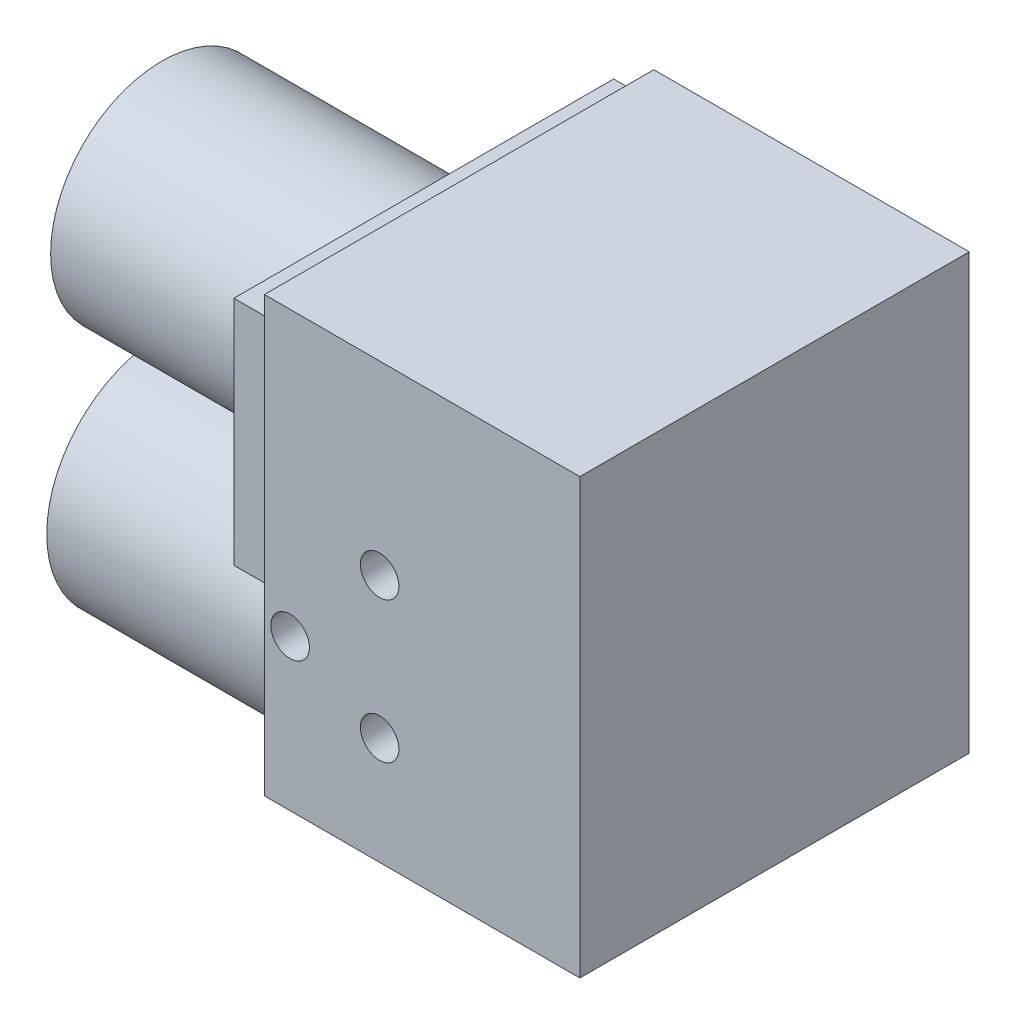
SolidWorks part; units mm, degrees
ref_plane "Front Plane" through (0, 0, 0) normal (0, 0, 1) x (1, 0, 0)
ref_plane "Top Plane" through (0, 0, 0) normal (0, 1, 0) x (1, 0, 0)
ref_plane "Right Plane" through (0, 0, 0) normal (1, 0, 0) x (0, 0, -1)
sketch "Sketch2" plane through (0, 0, 0) normal (0, 0, 1) x (1, 0, 0)
  line L1 (-49.09, 67.575) -> (49.09, 67.575)
  line L2 (-49.09, 67.575) -> (-49.09, -67.575)
  line L3 (-49.09, -67.575) -> (49.09, -67.575)
  line L4 (49.09, 67.575) -> (49.09, -67.575)
  point P4 (0, 67.575)
  point P6 (-49.09, 0)
  dimension "D1" = 135.15
  dimension "D2" = 98.18
extrude "Boss-Extrude1" add sketch "Sketch2" along normal blind 55.6 and the other way blind 65.6
sketch "Sketch3" plane through (-49.09, 0, 0) normal (-1, 0, 0) x (0, 0, 1)
  line L0 (-65.6, 67.575) -> (55.6, 67.575) construction
  circle A0 centre (0, 24.325) radius 34.65
  circle A1 centre (0, -50.675) radius 35.85
  point P4 (0, 0)
  point P8 (0, -38.3038)
  point P10 (0, 0)
  point P11 (-5, 24.575)
  point P12 (0, 0)
  point P13 (-5, 24.575)
  point P14 (-5, 24.575)
  point P15 (-5, 87.2668)
  point P16 (0, 0)
  point P17 (0, 0)
  point P18 (0, 18.7737)
  point P19 (0, 0)
  point P20 (0, 0)
  dimension "D1" = 69.3
  dimension "D3" = 75
  dimension "D4" = 71.7
  dimension "D2" = 43.25
extrude "Boss-Extrude2" add sketch "Sketch3" along normal blind 87.5
hole_wizard "Tap Drill for M14x2.0 Tap1" positions "Sketch5" profile "Sketch4" hole size "M14x2.0" standard "ANSI Metric"
sketch "Sketch5" plane through (0, 0, 55.6) normal (0, 0, 1) x (1, 0, 0)
  line L0 (-49.09, -67.575) -> (49.09, -67.575) construction
  line L1 (-49.09, 67.575) -> (-49.09, -67.575) construction
  point P0 (-13.23, 9.825)
  point P1 (-13.23, -34.075)
  point P3 (-41.09, -20.575)
  point P6 (10.8119, 15.3653)
  point P7 (0, 0)
  point P12 (0, 0)
  point P13 (0, -67.575)
  point P14 (0, 0)
  dimension "D1" = 33.5
  dimension "D2" = 35.86
  dimension "D3" = 77.4
  dimension "D4" = 8
  dimension "D5" = 47
sketch "Sketch4" plane through (-13.23, 9.825, 55.6) normal (1, 0, 0) x (0, -1, 0)
  line L0 (0, 0) -> (0, 23.1652)
  line L1 (0, 23.1652) -> (6, 19.56)
  line L2 (6, 19.56) -> (6, 0)
  line L5 (6, 0) -> (0, 0)
  line L10 (0, 23.1652) -> (-6, 19.56) construction
  line L11 (0, -6.35) -> (0, 107.95) construction
  dimension "Hole Dia." = 12
  dimension "Hole Depth" = 19.56
  dimension "Drill Angle" = 118
hole_wizard "Tap Drill for M12x1.5 Tap2" positions "Sketch6" profile "Sketch7" hole size "M12x1.5" standard "ANSI Metric"
sketch "Sketch6" plane through (0, -67.575, 0) normal (0, -1, 0) x (-1, 0, 0)
  line L0 (49.09, -55.6) -> (-49.09, -55.6) construction
  line L1 (49.09, -31.6166) -> (49.09, -55.6) construction
  line L2 (49.09, 65.6) -> (49.09, 31.6166) construction
  line L3 (49.09, 65.6) -> (-49.09, 65.6) construction
  point P0 (32.79, -35.1)
  point P2 (36.39, 57.2)
  dimension "D1" = 20.5
  dimension "D2" = 16.3
  dimension "D3" = 12.7
  dimension "D4" = 8.4
sketch "Sketch7" plane through (-32.79, -67.575, 35.1) normal (1, 0, 0) x (0, 0, -1)
  line L0 (0, 0) -> (0, 22.7145)
  line L1 (0, 22.7145) -> (5.25, 19.56)
  line L2 (5.25, 19.56) -> (5.25, 0)
  line L5 (5.25, 0) -> (0, 0)
  line L10 (0, 22.7145) -> (-5.25, 19.56) construction
  line L11 (0, -6.35) -> (0, 107.95) construction
  dimension "Hole Dia." = 10.5
  dimension "Hole Depth" = 19.56
  dimension "Drill Angle" = 118
sketch "Sketch8" plane through (-49.09, 0, 0) normal (-1, 0, 0) x (0, 0, 1)
  line L0 (55.6, 67.575) -> (55.6, -67.575) construction
  line L1 (-64.1, 60.325) -> (54.1, 60.325)
  line L2 (-64.1, 60.325) -> (-64.1, -11.675)
  line L3 (-64.1, -11.675) -> (54.1, -11.675)
  line L4 (54.1, 60.325) -> (54.1, -11.675)
  line L5 (-65.6, 67.575) -> (-65.6, -67.575) construction
  line L6 (-65.6, 67.575) -> (55.6, 67.575) construction
  circle A0 centre (0, 24.325) radius 34.65 construction
  circle A1 centre (0, 24.325) radius 34.65 construction
  dimension "D2" = 36
  dimension "D1" = 36
  dimension "D3" = 1.5
  dimension "D4" = 1.5
  dimension "D5" = 7.25
extrude "Boss-Extrude3" add sketch "Sketch8" along normal blind 11
hole_wizard "Tap Drill for M12x1.5 Tap3" positions "Sketch9" profile "Sketch10" hole size "M12x1.5" standard "ANSI Metric"
sketch "Sketch9" plane through (-60.09, 0, 0) normal (-1, 0, 0) x (0, 0, 1)
  line L0 (-65.6, 67.575) -> (55.6, 67.575) construction
  line L1 (55.6, 67.575) -> (55.6, -67.575) construction
  line L2 (-65.6, 67.575) -> (-65.6, -67.575) construction
  point P0 (-49.6, 52.175)
  point P2 (-55.1, 6.075)
  point P4 (45.1, 6.075)
  point P6 (39.6, 52.175)
  point P9 (0, 0)
  point P10 (0, 0)
  point P11 (0, 0)
  dimension "D1" = 15.4
  dimension "D2" = 16
  dimension "D3" = 16
  dimension "D4" = 61.5
  dimension "D5" = 10.5
  dimension "D6" = 10.5
sketch "Sketch10" plane through (-60.09, 52.175, -49.6) normal (0, 1, 0) x (0, 0, 1)
  line L0 (0, 0) -> (0, 22.7145)
  line L1 (0, 22.7145) -> (5.25, 19.56)
  line L2 (5.25, 19.56) -> (5.25, 0)
  line L5 (5.25, 0) -> (0, 0)
  line L10 (0, 22.7145) -> (-5.25, 19.56) construction
  line L11 (0, -6.35) -> (0, 107.95) construction
  dimension "Hole Dia." = 10.5
  dimension "Hole Depth" = 19.56
  dimension "Drill Angle" = 118
